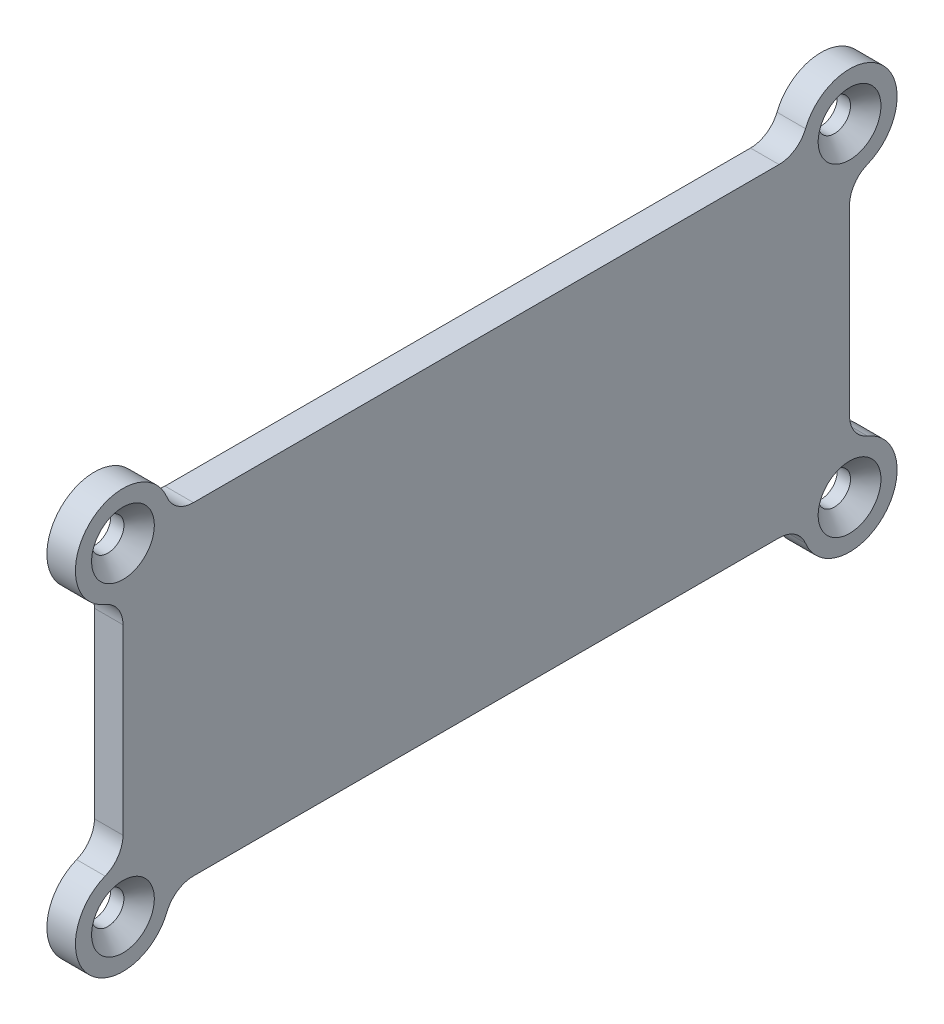
SolidWorks part; units mm, degrees
ref_plane "前视基准面" through (0, 0, 0) normal (0, 0, 1) x (1, 0, 0)
ref_plane "上视基准面" through (0, 0, 0) normal (0, 1, 0) x (1, 0, 0)
ref_plane "右视基准面" through (0, 0, 0) normal (1, 0, 0) x (0, 0, -1)
sketch "草图1" plane through (0, 0, 0) normal (1, 0, 0) x (0, 0, -1)
  line L0 (-38.2, 12) -> (-38.2, -12)
  line L1 (-38.2, 17) -> (38.2, 17) construction
  line L2 (-38.2, 17) -> (-38.2, -17) construction
  line L3 (-38.2, -17) -> (38.2, -17) construction
  line L4 (38.2, 17) -> (38.2, -17) construction
  line L5 (-38.2, 17) -> (38.2, -17) construction
  line L6 (-38.2, -17) -> (38.2, 17) construction
  line L7 (-33.2, -17) -> (33.2, -17)
  line L8 (38.2, -12) -> (38.2, 12)
  line L9 (33.2, 17) -> (-33.2, 17)
  line L10 (27.5, 5) -> (-27.5, 5) construction
  line L11 (-38.2, 17) -> (38.2, -17) construction
  line L12 (-38.2, -17) -> (38.2, 17) construction
  line L13 (0, 27.844) -> (0, -32.2494) construction
  circle A0 centre (-38.2, -17) radius 1.5 construction
  circle A1 centre (38.2, -17) radius 1.5 construction
  circle A2 centre (38.2, 17) radius 1.5 construction
  circle A3 centre (-38.2, 17) radius 1.5 construction
  arc A4 (-38.2, -12) -> (-33.2, -17) centre (-38.2, -17) ccw
  arc A5 (-33.2, 17) -> (-38.2, 12) centre (-38.2, 17) ccw
  arc A6 (38.2, 12) -> (33.2, 17) centre (38.2, 17) ccw
  arc A7 (33.2, -17) -> (38.2, -12) centre (38.2, -17) ccw
  circle A8 centre (27.5, 5) radius 4.25 construction
  circle A9 centre (-27.5, 5) radius 4.25 construction
  point P0 (0, 0)
  point P10 (0, 0)
  dimension "D3" = 3
  dimension "D4" = 10
  dimension "D5" = 8.5
  dimension "D1" = 76.4
  dimension "D2" = 34
  dimension "D6" = 55
  dimension "D7" = 12
extrude "凸台-拉伸1" add sketch "草图1" along normal blind 3
fillet "圆角1" radius 3 8 edges at (1.5, -17, -33.2) (1.5, -12, -38.2) (1.5, 12, -38.2) (1.5, 17, -33.2) (1.5, 17, 33.2) (1.5, -17, 33.2) (1.5, -12, 38.2) (1.5, 12, 38.2)
hole_wizard "打孔尺寸(%根据十字)槽半沉头木螺钉的类型1" positions "3D草图1" profile "草图2" countersink size "M3" standard "GB" end condition through all
sketch3d "3D草图1"
  line L0 (3, 17, 38.2) -> (0, 17, 38.2) construction
  line L1 (3, -17, 38.2) -> (0, -17, 38.2) construction
  line L2 (3, -17, -38.2) -> (0, -17, -38.2) construction
  line L3 (3, 17, -38.2) -> (0, 17, -38.2) construction
  point P0 (3, 17, 38.2)
  point P4 (3, -17, 38.2)
  point P8 (3, -17, -38.2)
  point P12 (3, 17, -38.2)
sketch "草图2" plane through (3, 17, 38.2) normal (0, 1, 0) x (0, 0, -1)
  line L0 (0, 0) -> (0, 3)
  line L1 (0, 3) -> (1.7, 3)
  line L2 (1.7, 3) -> (1.7, 1.6)
  line L3 (1.7, 1.6) -> (3.3, 0)
  line L5 (3.3, 0) -> (0, 0)
  line L6 (-1.7, 1.6) -> (-3.3, 0) construction
  line L11 (0, -6.35) -> (0, 107.95) construction
  dimension "通孔孔直径" = 3.4
  dimension "通孔孔深度" = 3
  dimension "近端锥形沉头孔直径" = 6.6
  dimension "近端锥形沉头孔角度" = 90
sketch "草图3" plane through (3, 0, 0) normal (1, 0, 0) x (0, 0, -1)
  line L0 (27.5, 5) -> (-27.5, 5) construction
  line L1 (27.5, 5) -> (-27.5, 5) construction
  circle A0 centre (27.5, 5) radius 4.25 construction
  circle A1 centre (-27.5, 5) radius 4.25 construction
  circle A2 centre (27.5, 5) radius 4.25 construction
  circle A3 centre (-27.5, 5) radius 4.25 construction
